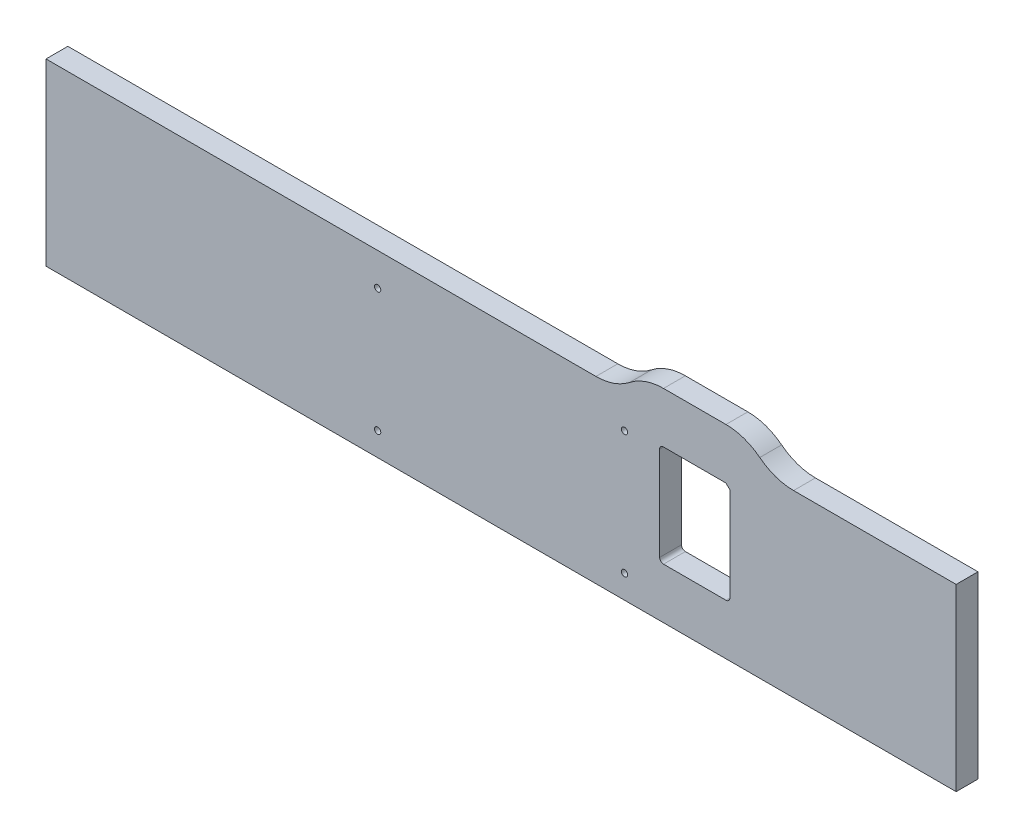
SolidWorks part; units mm, degrees
material "Pine"
ref_plane "Front Plane" through (0, 0, 0) normal (0, 0, 1) x (1, 0, 0)
ref_plane "Top Plane" through (0, 0, 0) normal (0, 1, 0) x (1, 0, 0)
ref_plane "Right Plane" through (0, 0, 0) normal (1, 0, 0) x (0, 0, -1)
sketch "Sketch1" plane through (0, 0, 0) normal (0, 0, 1) x (1, 0, 0)
  line L0 (-163.9887, -5335.905) -> (-163.9887, -5432.425)
  line L1 (-102.87, -5350.891) -> (-33.02, -5350.891)
  line L2 (-111.8235, -5341.9375) -> (-111.8235, -5334)
  line L3 (-24.0665, -5341.9375) -> (-24.0665, -5334)
  line L4 (-298.9262, -5332.73) -> (-167.1637, -5332.73)
  line L5 (-167.1637, -5435.6) -> (-298.9262, -5435.6)
  line L6 (-302.1012, -5432.425) -> (-302.1012, -5335.905)
  line L7 (-107.6325, -5329.809) -> (-28.2575, -5329.809)
  line L8 (174.9425, -5308.6) -> (174.9425, -5581.65)
  line L9 (449.2625, -5413.1661) -> (449.2625, -5421.9659)
  line L10 (595.3125, -5421.9659) -> (595.3125, -5413.1661)
  line L11 (839.47, -5509.5521) -> (839.47, -5307.6729)
  line L12 (839.47, -5307.6729) -> (863.6, -5307.6729)
  line L13 (839.47, -5509.5521) -> (863.6, -5509.5521)
  line L14 (863.6, -5509.5521) -> (863.6, -5307.6729)
  line L15 (-354.2665, -5341.9375) -> (-354.2665, -5334)
  line L16 (-100.8856, -5889.625) -> (-50.0856, -5889.625)
  line L17 (-104.0606, -5969) -> (-104.0606, -5892.8)
  line L18 (-46.9106, -5892.8) -> (-46.9106, -5969)
  line L19 (-50.0856, -5972.175) -> (-100.8856, -5972.175)
  line L20 (-100.8856, -5848.35) -> (-50.0856, -5848.35)
  line L21 (857.25, -5502.275) -> (157.1625, -5575.3)
  line L22 (857.25, -5314.95) -> (857.25, -5502.275)
  line L23 (157.1625, -5314.95) -> (157.1625, -5575.3)
  line L24 (857.25, -5314.95) -> (157.1625, -5314.95)
  line L25 (150.8125, -5308.6) -> (174.9425, -5308.6)
  line L26 (174.9425, -5581.65) -> (150.8125, -5581.65)
  line L27 (137.16, -5314.95) -> (137.16, -5502.275)
  line L28 (150.8125, -5581.65) -> (150.8125, -5308.6)
  line L29 (590.8224, -5408.676) -> (453.7526, -5408.676)
  line L30 (453.7526, -5426.456) -> (590.8224, -5426.456)
  line L31 (137.16, -6013.45) -> (137.16, -5867.4)
  line L32 (150.8125, -5746.75) -> (150.8125, -6019.8)
  line L33 (143.51, -5639.9938) -> (143.51, -5654.294)
  line L34 (590.8224, -5919.724) -> (453.7526, -5919.724)
  line L35 (453.7526, -5901.944) -> (590.8224, -5901.944)
  line L36 (449.2625, -5915.2339) -> (449.2625, -5906.4341)
  line L37 (174.9425, -6019.8) -> (174.9425, -5746.75)
  line L38 (595.3125, -5906.4341) -> (595.3125, -5915.2339)
  line L39 (839.47, -5818.8479) -> (839.47, -6020.7271)
  line L40 (839.47, -5818.8479) -> (863.6, -5818.8479)
  line L41 (863.6, -5818.8479) -> (863.6, -6020.7271)
  line L42 (839.47, -6020.7271) -> (863.6, -6020.7271)
  line L43 (-155.8782, -5867.4) -> (-603.25, -5867.4)
  line L44 (-433.07, -5350.891) -> (-363.22, -5350.891)
  line L45 (-437.8325, -5329.809) -> (-358.4575, -5329.809)
  line L46 (889, -6045.2) -> (-635, -6045.2)
  line L47 (-635, -5283.2) -> (889, -5283.2)
  line L48 (-635, -6045.2) -> (-635, -5283.2)
  line L49 (889, -5283.2) -> (889, -6045.2)
  line L50 (137.16, -5502.275) -> (-603.25, -5502.275)
  line L51 (-603.25, -5314.95) -> (137.16, -5314.95)
  line L52 (143.51, -5654.294) -> (-609.6, -5654.294)
  line L53 (-609.6, -5639.9938) -> (143.51, -5639.9938)
  line L54 (137.16, -5536.0062) -> (-603.25, -5536.0062)
  line L55 (-603.25, -5794.375) -> (137.16, -5794.375)
  line L56 (-603.25, -6013.45) -> (137.16, -6013.45)
  line L57 (-603.25, -5536.0062) -> (-603.25, -5794.375)
  line L58 (137.16, -5794.375) -> (137.16, -5536.0062)
  line L59 (-609.6, -5654.294) -> (-609.6, -5639.9938)
  line L60 (-603.25, -5867.4) -> (-603.25, -6013.45)
  line L61 (-603.25, -5314.95) -> (-603.25, -5502.275)
  line L62 (-442.0235, -5341.9375) -> (-442.0235, -5334)
  line L63 (857.25, -5826.125) -> (157.1625, -5753.1)
  line L64 (857.25, -6013.45) -> (857.25, -5826.125)
  line L65 (157.1625, -6013.45) -> (157.1625, -5753.1)
  line L66 (857.25, -6013.45) -> (157.1625, -6013.45)
  line L67 (174.9425, -5746.75) -> (150.8125, -5746.75)
  line L68 (150.8125, -6019.8) -> (174.9425, -6019.8)
  line L69 (137.16, -5867.4) -> (4.907, -5867.4)
  circle A0 centre (-36.195, -5484.0124) radius 1.5875
  arc A1 (-298.9262, -5332.73) -> (-302.1012, -5335.905) centre (-298.9262, -5335.905) ccw
  arc A2 (-302.1012, -5432.425) -> (-298.9262, -5435.6) centre (-298.9262, -5432.425) ccw
  arc A3 (-163.9887, -5335.905) -> (-167.1637, -5332.73) centre (-167.1637, -5335.905) ccw
  arc A4 (-167.1637, -5435.6) -> (-163.9887, -5432.425) centre (-167.1637, -5432.425) ccw
  arc A5 (-111.8235, -5341.9375) -> (-102.87, -5350.891) centre (-102.87, -5341.9375) ccw
  arc A6 (-107.6325, -5329.809) -> (-111.8235, -5334) centre (-107.6325, -5334) ccw
  circle A7 centre (166.0525, -5444.6613) radius 1.5875
  circle A8 centre (166.0525, -5358.1871) radius 1.5875
  circle A9 centre (471.4875, -5417.566) radius 1.5875
  arc A10 (453.7526, -5408.676) -> (449.2625, -5413.1661) centre (451.5076, -5410.9211) ccw
  arc A11 (449.2625, -5421.9659) -> (453.7526, -5426.456) centre (451.5076, -5424.2109) ccw
  circle A12 centre (522.2875, -5417.566) radius 1.5875
  circle A13 centre (573.0875, -5417.566) radius 1.5875
  arc A14 (590.8224, -5426.456) -> (595.3125, -5421.9659) centre (593.0674, -5424.2109) ccw
  arc A15 (595.3125, -5413.1661) -> (590.8224, -5408.676) centre (593.0674, -5410.9211) ccw
  circle A16 centre (848.36, -5471.8269) radius 1.5875
  circle A17 centre (848.36, -5409.0762) radius 1.5875
  circle A18 centre (848.36, -5346.3254) radius 1.5875
  arc A19 (-363.22, -5350.891) -> (-354.2665, -5341.9375) centre (-363.22, -5341.9375) ccw
  arc A20 (-354.2665, -5334) -> (-358.4575, -5329.809) centre (-358.4575, -5334) ccw
  arc A21 (-24.0665, -5334) -> (-28.2575, -5329.809) centre (-28.2575, -5334) ccw
  arc A22 (-33.02, -5350.891) -> (-24.0665, -5341.9375) centre (-33.02, -5341.9375) ccw
  circle A23 centre (-86.995, -5484.0124) radius 1.5875
  circle A24 centre (-333.4544, -5894.07) radius 2.54
  circle A25 centre (-333.4544, -5994.4) radius 2.54
  arc A26 (-104.0606, -5969) -> (-100.8856, -5972.175) centre (-100.8856, -5969) ccw
  arc A27 (-50.0856, -5972.175) -> (-46.9106, -5969) centre (-50.0856, -5969) ccw
  arc A28 (-100.8856, -5848.35) -> (-128.3819, -5857.875) centre (-100.8856, -5892.8) ccw
  arc A29 (-155.8782, -5867.4) -> (-128.3819, -5857.875) centre (-155.8782, -5822.95) ccw
  arc A30 (-22.5893, -5857.875) -> (-50.0856, -5848.35) centre (-50.0856, -5892.8) ccw
  circle A31 centre (-132.6356, -5894.07) radius 2.54
  circle A32 centre (-132.6356, -5994.4) radius 2.54
  arc A33 (-46.9106, -5892.8) -> (-50.0856, -5889.625) centre (-50.0856, -5892.8) ccw
  arc A34 (-100.8856, -5889.625) -> (-104.0606, -5892.8) centre (-100.8856, -5892.8) ccw
  arc A35 (-22.5893, -5857.875) -> (4.907, -5867.4) centre (4.907, -5822.95) ccw
  circle A36 centre (166.0525, -5531.1356) radius 1.5875
  arc A37 (449.2625, -5915.2339) -> (453.7526, -5919.724) centre (451.5076, -5917.4789) ccw
  arc A38 (453.7526, -5901.944) -> (449.2625, -5906.4341) centre (451.5076, -5904.1891) ccw
  circle A39 centre (166.0525, -5797.2644) radius 1.5875
  circle A40 centre (166.0525, -5883.7387) radius 1.5875
  circle A41 centre (166.0525, -5970.2129) radius 1.5875
  circle A42 centre (471.4875, -5910.834) radius 1.5875
  circle A43 centre (522.2875, -5910.834) radius 1.5875
  circle A44 centre (573.0875, -5910.834) radius 1.5875
  arc A45 (595.3125, -5906.4341) -> (590.8224, -5901.944) centre (593.0674, -5904.1891) ccw
  arc A46 (590.8224, -5919.724) -> (595.3125, -5915.2339) centre (593.0674, -5917.4789) ccw
  circle A47 centre (848.36, -5919.3238) radius 1.5875
  circle A48 centre (848.36, -5982.0746) radius 1.5875
  circle A49 centre (848.36, -5856.5731) radius 1.5875
  arc A50 (-437.8325, -5329.809) -> (-442.0235, -5334) centre (-437.8325, -5334) ccw
  circle A51 centre (-429.895, -5484.0124) radius 1.5875
  arc A52 (-442.0235, -5341.9375) -> (-433.07, -5350.891) centre (-433.07, -5341.9375) ccw
  circle A53 centre (-379.095, -5484.0124) radius 1.5875
sketch "HeadDisplayBraceOutline" plane through (0, 0, 0) normal (0, 0, 1) x (1, 0, 0)
  line L0 (137.16, -6013.45) -> (-603.25, -6013.45)
  line L1 (-603.25, -6013.45) -> (-603.25, -5867.4)
  line L2 (-603.25, -5867.4) -> (-155.8782, -5867.4)
  line L3 (-100.8856, -5848.35) -> (-50.0856, -5848.35)
  line L4 (4.907, -5867.4) -> (137.16, -5867.4)
  line L5 (137.16, -5867.4) -> (137.16, -6013.45)
  arc A0 (-155.8782, -5867.4) -> (-128.3819, -5857.875) centre (-155.8782, -5822.95) ccw
  arc A1 (-128.3819, -5857.875) -> (-100.8856, -5848.35) centre (-100.8856, -5892.8) cw
  arc A2 (-50.0856, -5848.35) -> (-22.5893, -5857.875) centre (-50.0856, -5892.8) cw
  arc A3 (-22.5893, -5857.875) -> (4.907, -5867.4) centre (4.907, -5822.95) ccw
extrude "HeadDisplayBracket_Thickness" add sketch "HeadDisplayBraceOutline" against normal blind 17.78
sketch "Sketch3" plane through (0, 0, 0) normal (0, 0, 1) x (1, 0, 0)
  line L0 (-104.0606, -5892.8) -> (-104.0606, -5969)
  line L1 (-100.8856, -5972.175) -> (-50.0856, -5972.175)
  line L2 (-46.9106, -5969) -> (-46.9106, -5892.8)
  line L3 (-46.9106, -5892.8) -> (-50.0856, -5889.625)
  line L4 (-50.0856, -5889.625) -> (-100.8856, -5889.625)
  circle A0 centre (-333.4544, -5994.4) radius 2.54
  circle A1 centre (-132.6356, -5994.4) radius 2.54
  circle A2 centre (-132.6356, -5894.07) radius 2.54
  circle A3 centre (-333.4544, -5894.07) radius 2.54
  arc A4 (-104.0606, -5969) -> (-100.8856, -5972.175) centre (-100.8856, -5969) ccw
  arc A5 (-50.0856, -5972.175) -> (-46.9106, -5969) centre (-50.0856, -5969) ccw
  arc A6 (-100.8856, -5889.625) -> (-104.0606, -5892.8) centre (-100.8856, -5892.8) ccw
extrude "Cut-Extrude1" cut sketch "Sketch3" against normal up to surface (17.78 mm away) up to face at (-138.5094, -5890.895, -17.78)
